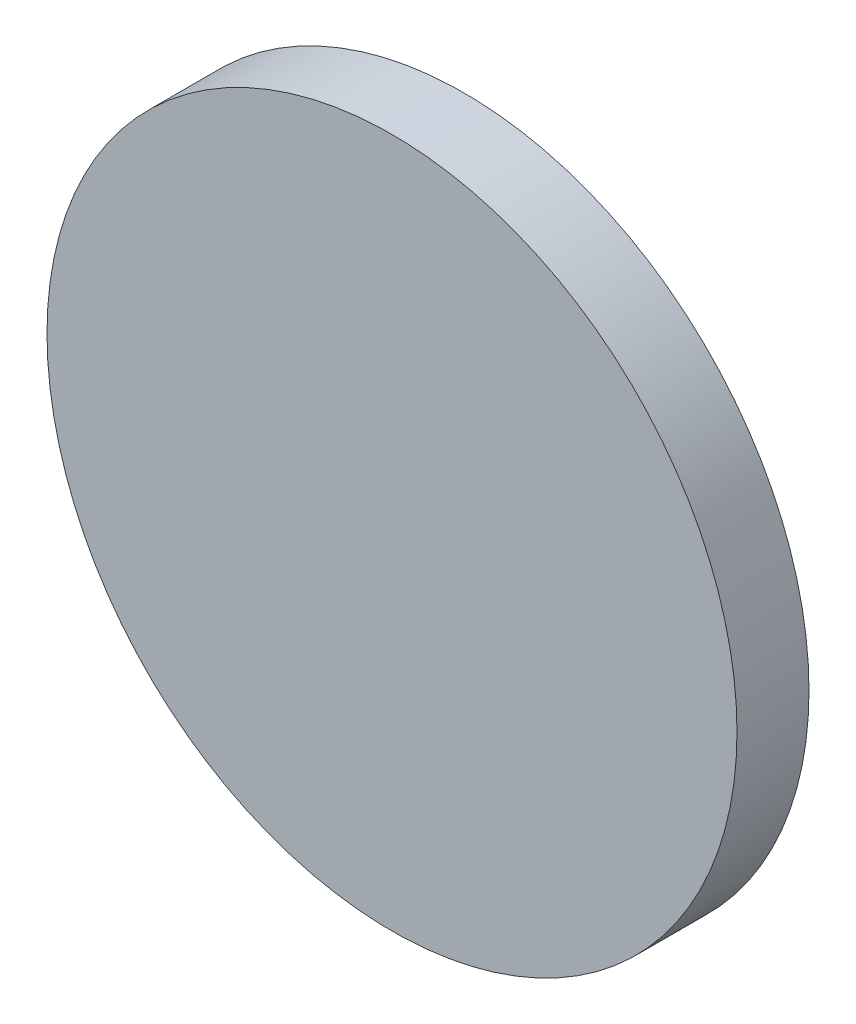
SolidWorks part; units mm, degrees
ref_plane "Front Plane" through (0, 0, 0) normal (0, 0, 1) x (1, 0, 0)
ref_plane "Top Plane" through (0, 0, 0) normal (0, 1, 0) x (1, 0, 0)
ref_plane "Right Plane" through (0, 0, 0) normal (1, 0, 0) x (0, 0, -1)
sketch "Sketch1" plane through (0, 0, 0) normal (0, 0, 1) x (1, 0, 0)
  circle A0 centre (0, 0) radius 115
  dimension "D1" = 230
extrude "Boss-Extrude1" add sketch "Sketch1" along normal blind 24
